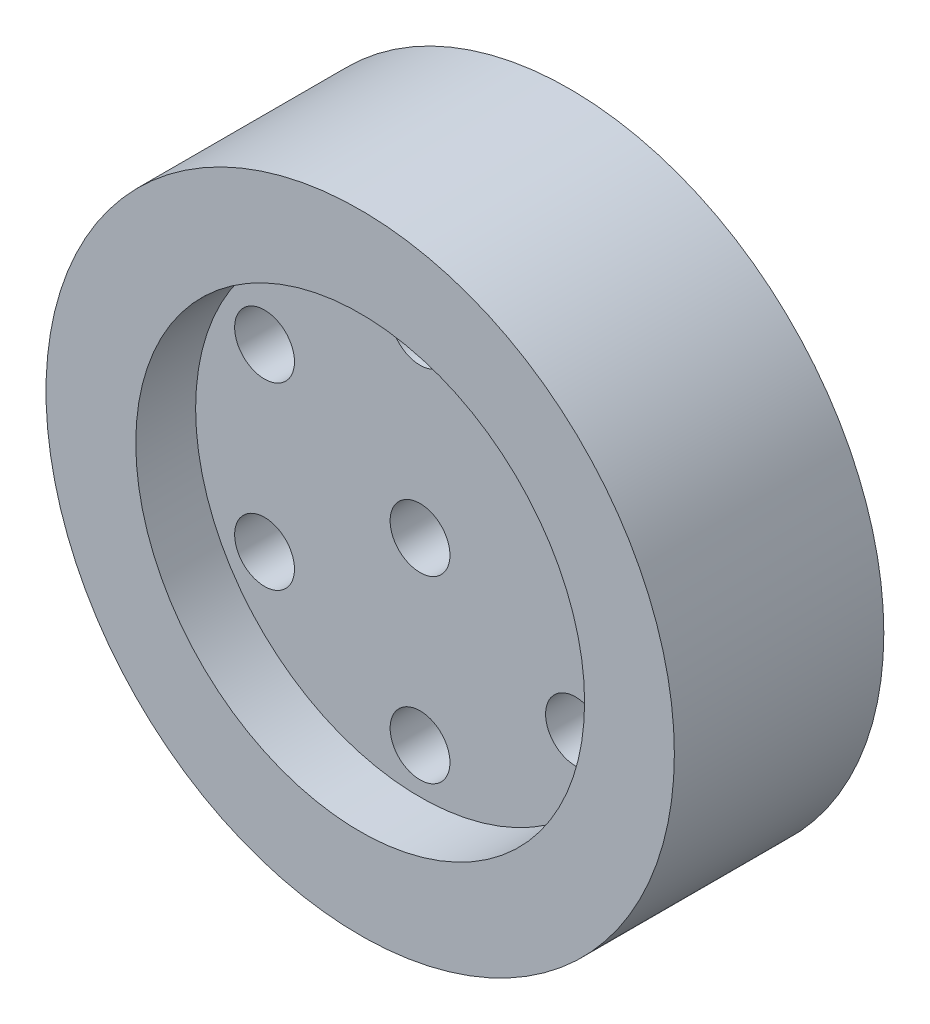
SolidWorks part; units mm, degrees
ref_plane "Front Plane" through (0, 0, 0) normal (0, 0, 1) x (1, 0, 0)
ref_plane "Top Plane" through (0, 0, 0) normal (0, 1, 0) x (1, 0, 0)
ref_plane "Right Plane" through (0, 0, 0) normal (1, 0, 0) x (0, 0, -1)
sketch "Sketch1" plane through (0, 0, 0) normal (0, 0, 1) x (1, 0, 0)
  circle A0 centre (0, 0) radius 21
  circle A1 centre (0, 0) radius 12 construction
  circle A2 centre (0, 12) radius 2
  circle A3 centre (0, 0) radius 12 construction
  circle A4 centre (10.3923, 6) radius 2
  circle A5 centre (0, 0) radius 12 construction
  circle A6 centre (10.3923, -6) radius 2
  circle A7 centre (0, 0) radius 12 construction
  circle A8 centre (0, -12) radius 2
  circle A9 centre (0, 0) radius 12 construction
  circle A10 centre (-10.3923, -6) radius 2
  circle A11 centre (0, 0) radius 12 construction
  circle A12 centre (-10.3923, 6) radius 2
  circle A13 centre (0, 0) radius 2
  point P23 (0, 0)
  dimension "D1" = 42
  dimension "D2" = 24
  dimension "D3" = 4
  dimension "D4" = 6
extrude "Boss-Extrude1" add sketch "Sketch1" along normal blind 14
sketch "Sketch2" plane through (0, 0, 14) normal (0, 0, 1) x (1, 0, 0)
  circle A0 centre (0, 0) radius 15
  dimension "D1" = 30
extrude "Cut-Extrude1" cut sketch "Sketch2" against normal blind 4
sketch "Sketch3" plane through (0, 0, 0) normal (0, 0, -1) x (-1, 0, 0)
  circle A0 centre (0, 0) radius 15
  circle A1 centre (0, 0) radius 5
  dimension "D1" = 30
  dimension "D2" = 10
extrude "Cut-Extrude2" cut sketch "Sketch3" against normal blind 4
